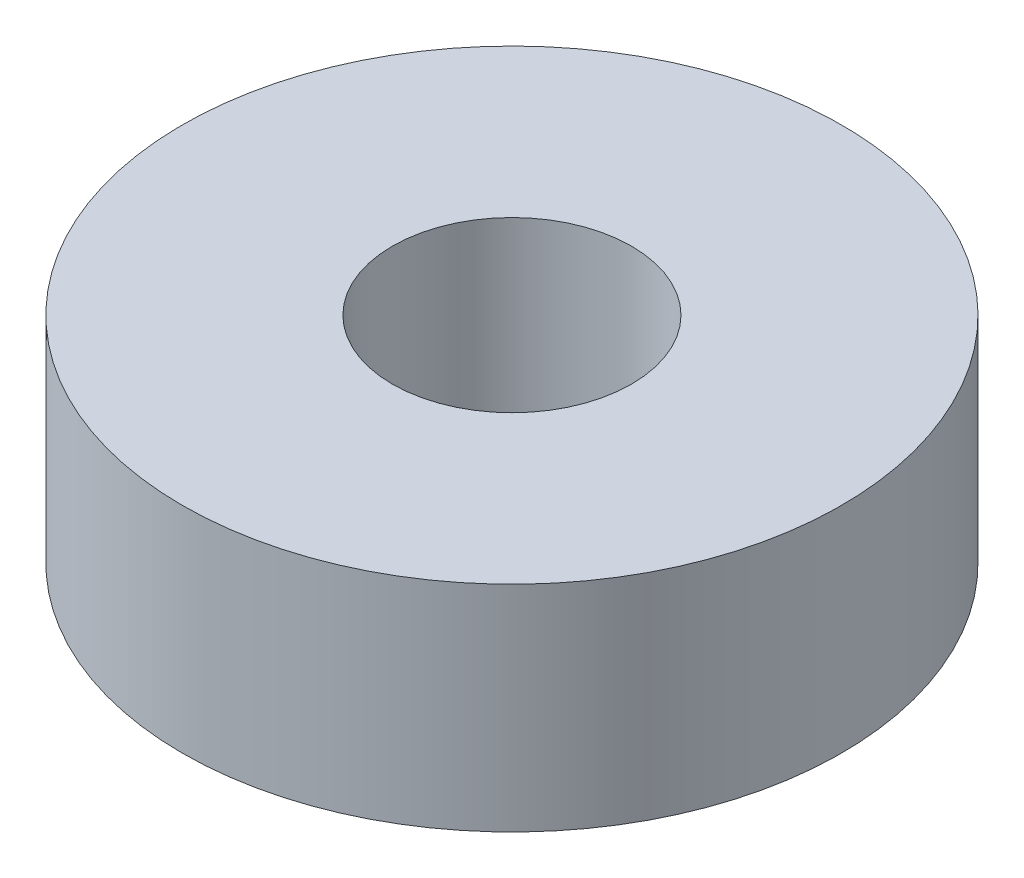
SolidWorks part; units mm, degrees
ref_plane "Front Plane" through (0, 0, 0) normal (0, 0, 1) x (1, 0, 0)
ref_plane "Top Plane" through (0, 0, 0) normal (0, 1, 0) x (1, 0, 0)
ref_plane "Right Plane" through (0, 0, 0) normal (1, 0, 0) x (0, 0, -1)
sketch "Sketch1" plane through (0, 0, 0) normal (0, 1, 0) x (1, 0, 0)
  circle A0 centre (0, 0) radius 3.9
  circle A1 centre (0, 0) radius 10.75
  dimension "D1" = 21.5
  dimension "D2" = 7.8
extrude "Boss-Extrude1" add sketch "Sketch1" along normal blind 7
